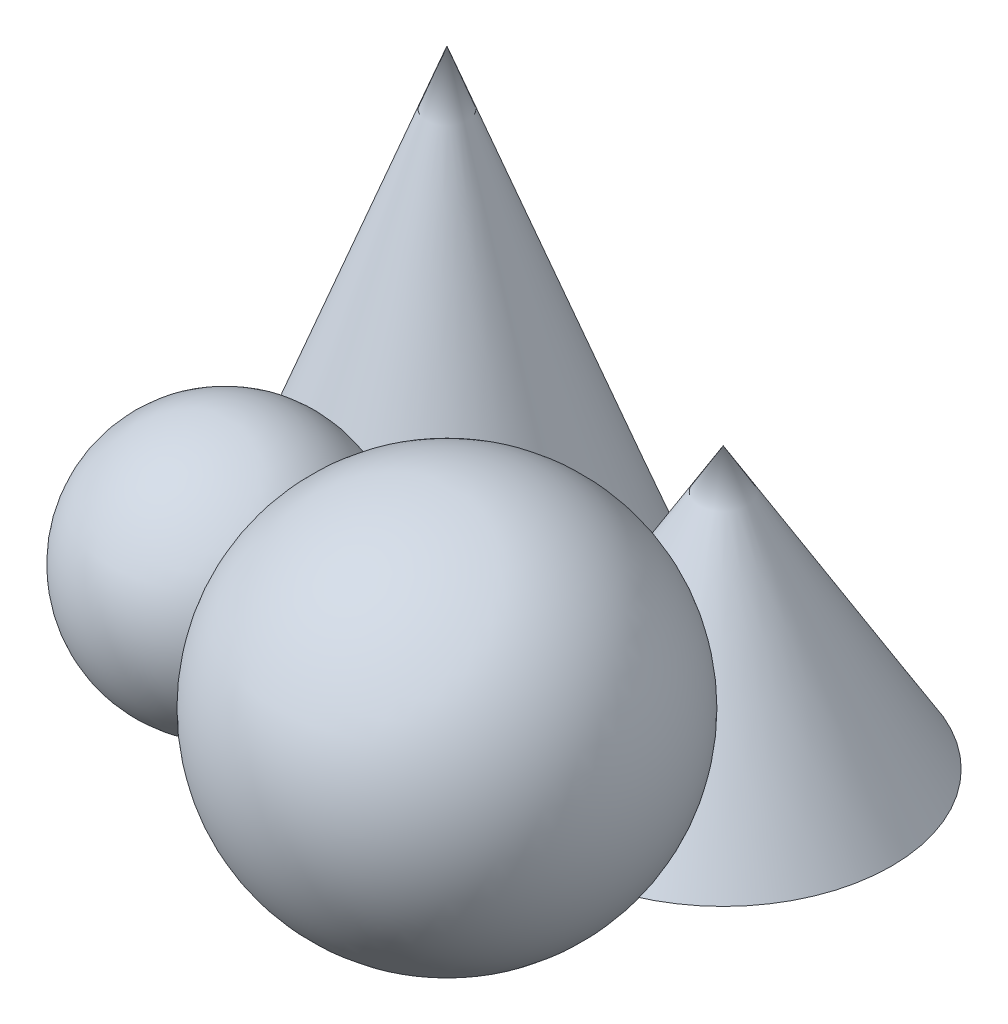
SolidWorks part; units mm, degrees
ref_plane "Front" through (0, 0, 0) normal (0, 0, 1) x (1, 0, 0)
ref_plane "Top" through (0, 0, 0) normal (0, 1, 0) x (1, 0, 0)
ref_plane "Right" through (0, 0, 0) normal (1, 0, 0) x (0, 0, -1)
sketch "Sketch1" plane through (0, 0, 0) normal (0, 1, 0) x (1, 0, 0)
  circle A0 centre (0, 0) radius 30
sketch "Sketch2" plane through (0, 0, 0) normal (0, 0, 1) x (1, 0, 0)
  point P0 (0, 80)
  dimension "D1" = 80
loft "ConeB" add profiles "Sketch2", "Sketch1"
sketch3d "3DSketch1"
  point P0 (60.1041, 35, 60.1041)
ref_plane "Plane1" through (0, 0, 60.1041) normal (0, 0, 1) x (1, 0, 0)
sketch "Sketch3" plane through (0, 0, 60.1041) normal (0, 0, 1) x (1, 0, 0)
  line L0 (60.1041, 70) -> (60.1041, 0)
  arc A0 (60.1041, 0) -> (60.1041, 70) centre (60.1041, 35) ccw
revolve "SphereA" add sketch "Sketch3" angle 360 about L0
sketch "Sketch4" plane through (0, 0, 0) normal (0, 1, 0) x (1, 0, 0)
  circle A0 centre (60.1041, -9.4562) radius 30.8469
ref_plane "Plane2" through (0, 0, 9.4562) normal (0, 0, 1) x (1, 0, 0)
sketch "Sketch5" plane through (0, 0, 9.4562) normal (0, 0, 1) x (1, 0, 0)
  line L0 (90.951, 0) -> (29.2572, 0) construction
  point P0 (60.1041, 51.3324)
  dimension "D1" = 51.3324
loft "ConeD" add profiles "Sketch4", "Sketch5"
sketch3d "3DSketch2"
  point P0 (5.058, 23.1169, 45.7412)
ref_plane "Plane3" through (0, 0, 45.7412) normal (0, 0, 1) x (1, 0, 0)
sketch "Sketch6" plane through (0, 0, 45.7412) normal (0, 0, 1) x (1, 0, 0)
  line L0 (5.058, 46.2338) -> (5.058, 0)
  arc A0 (5.058, 0) -> (5.058, 46.2338) centre (5.058, 23.1169) ccw
revolve "SphereC" add sketch "Sketch6" angle 360 about L0
